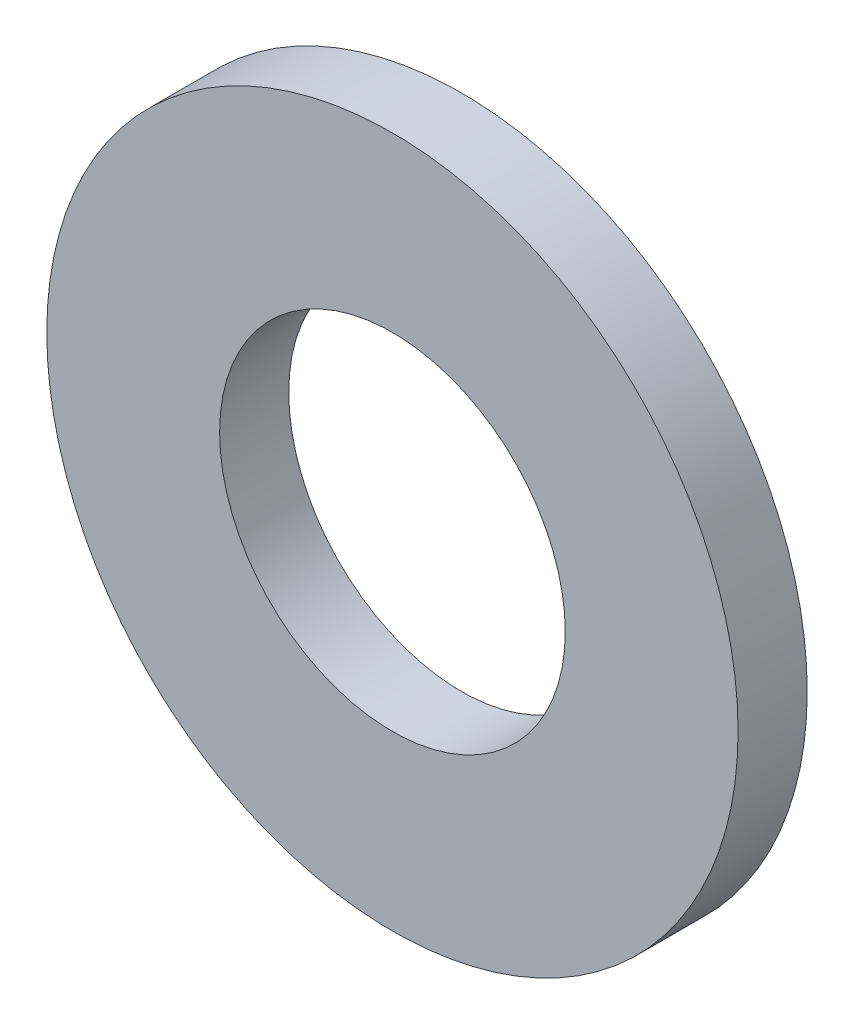
SolidWorks part; units mm, degrees
ref_plane "Plan de face" through (0, 0, 0) normal (0, 0, 1) x (1, 0, 0)
ref_plane "Plan de dessus" through (0, 0, 0) normal (0, 1, 0) x (1, 0, 0)
ref_plane "Plan de droite" through (0, 0, 0) normal (1, 0, 0) x (0, 0, -1)
sketch "Esquisse1" plane through (0, 0, 0) normal (0, 0, 1) x (1, 0, 0)
  circle A0 centre (0, 0) radius 5
  circle A1 centre (0, 0) radius 10
  dimension "D1" = 20
  dimension "D2" = 10
extrude "Boss.-Extru.1" add sketch "Esquisse1" along normal blind 2
